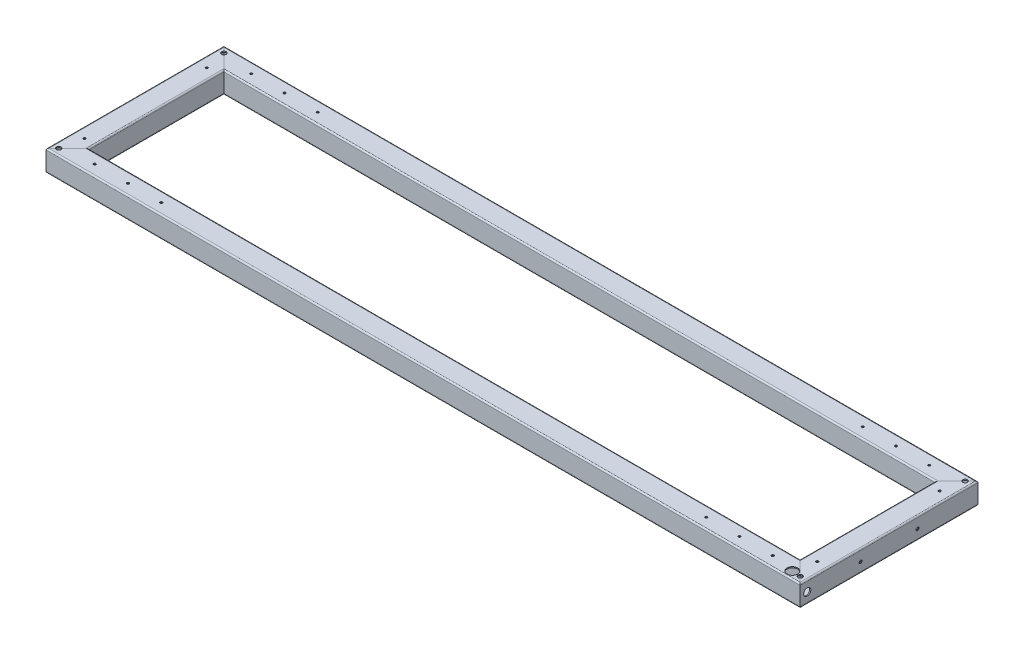
SolidWorks part; units mm, degrees
material "Unlegierter Baustahl"
ref_plane "Ebene vorne" through (0, 0, 0) normal (0, 0, 1) x (1, 0, 0)
ref_plane "Ebene oben" through (0, 0, 0) normal (0, 1, 0) x (1, 0, 0)
ref_plane "Ebene rechts" through (0, 0, 0) normal (1, 0, 0) x (0, 0, -1)
sketch "Skizze1" plane through (0, 0, 0) normal (0, 1, 0) x (1, 0, 0)
  line L1 (-1060, 250) -> (1060, 250)
  line L2 (-1060, 250) -> (-1060, -250)
  line L3 (-1060, -250) -> (1060, -250)
  line L4 (1060, 250) -> (1060, -250)
  line L5 (-1060, 250) -> (1060, -250) construction
  line L6 (-1060, -250) -> (1060, 250) construction
  point P0 (0, 0)
  dimension "D1" = 500
  dimension "D2" = 2120
other "Strukturbauteil1"
ref_plane "Ebene2" through (-1060, 0, -220) normal (1, 0, 0) x (0, 0, -1)
sketch "Skizze12" plane through (-1060, 0, -220) normal (1, 0, 0) x (0, 0, -1)
  line L0 (27, -26) -> (27, 26)
  line L1 (26, -30) -> (-26, -30)
  line L2 (30, -26) -> (30, 26)
  line L3 (26, 30) -> (-26, 30)
  line L4 (-30, -26) -> (-30, 26)
  line L5 (26, 27) -> (-26, 27)
  line L6 (-27, -26) -> (-27, 26)
  line L7 (26, -27) -> (-26, -27)
  line L8 (0, -30) -> (0, 30) construction
  arc A0 (-30, 26) -> (-26, 30) centre (-26, 26) cw
  arc A1 (-26, -30) -> (-30, -26) centre (-26, -26) cw
  arc A2 (30, -26) -> (26, -30) centre (26, -26) cw
  arc A3 (26, 30) -> (30, 26) centre (26, 26) cw
  arc A4 (26, 27) -> (27, 26) centre (26, 26) cw
  arc A5 (-27, 26) -> (-26, 27) centre (-26, 26) cw
  arc A6 (-26, -27) -> (-27, -26) centre (-26, -26) cw
  arc A7 (27, -26) -> (26, -27) centre (26, -26) cw
  point P4 (0, 30)
  point P5 (0, -30)
  point P10 (-30, -30)
  point P13 (30, -30)
  point P16 (30, 30)
  point P25 (-30, -30)
  point P26 (-30, 30)
  point P27 (30, 30)
  point P30 (30, -30)
  point P31 (0, 0)
  point P32 (-30, 0)
  point P33 (30, 0)
  point P34 (0, 0)
  dimension "D3" = 4
  dimension "D1" = 60
  dimension "D2" = 60
  dimension "D4" = 3
hole_wizard "M6 Gewindebohrung1" positions "Skizze16" profile "Skizze15" tap size "M6" standard "DIN" end condition up to next
sketch "Skizze16" plane through (0, 30, 0) normal (0, 1, 0) x (1, 0, 0)
  point P0 (1030, -172)
  point P3 (1030, 172)
sketch "Skizze15" plane through (1030, 30, 172) normal (1, 0, 0) x (0, 0, 1)
  line L0 (0, 0) -> (0, 3)
  line L1 (0, 3) -> (3.025, 3)
  line L2 (2.5, 2.475) -> (2.5, 0.75)
  line L3 (2.5, 0.75) -> (3.25, 0)
  line L5 (3.25, 0) -> (0, 0)
  line L6 (-2.5, 0.75) -> (-3.25, 0) construction
  line L7 (3.025, 3) -> (2.5, 2.475)
  line L8 (-3.025, 3) -> (-2.5, 2.475) construction
  line L11 (0, -6.35) -> (0, 107.95) construction
  dimension "Bohrerdurchmesser" = 5
  dimension "Bohrungstiefe" = 3
  dimension "Senkdurchmesser (Oben)" = 6.5
  dimension "Senkwinkel (Oben)" = 90
  dimension "Senkdurchmesser (Unten)" = 6.05
  dimension "Senkwinkel (Unten)" = 90
cosmetic thread "Bohrungsgewinde9" parameters "D2"=6
cosmetic thread "Bohrungsgewinde10" parameters "D2"=6
hole_wizard "M6 Gewindebohrung2" positions "Skizze18" profile "Skizze17" tap size "M6" standard "DIN" end condition up to next
sketch "Skizze18" plane through (0, 30, 0) normal (0, 1, 0) x (1, 0, 0)
  point P0 (-1030, 172)
  point P3 (-1030, -172)
sketch "Skizze17" plane through (-1030, 30, -172) normal (1, 0, 0) x (0, 0, 1)
  line L0 (0, 0) -> (0, 3)
  line L1 (0, 3) -> (3.025, 3)
  line L2 (2.5, 2.475) -> (2.5, 0.75)
  line L3 (2.5, 0.75) -> (3.25, 0)
  line L5 (3.25, 0) -> (0, 0)
  line L6 (-2.5, 0.75) -> (-3.25, 0) construction
  line L7 (3.025, 3) -> (2.5, 2.475)
  line L8 (-3.025, 3) -> (-2.5, 2.475) construction
  line L11 (0, -6.35) -> (0, 107.95) construction
  dimension "Bohrerdurchmesser" = 5
  dimension "Bohrungstiefe" = 3
  dimension "Senkdurchmesser (Oben)" = 6.5
  dimension "Senkwinkel (Oben)" = 90
  dimension "Senkdurchmesser (Unten)" = 6.05
  dimension "Senkwinkel (Unten)" = 90
cosmetic thread "Bohrungsgewinde11" parameters "D2"=6
cosmetic thread "Bohrungsgewinde12" parameters "D2"=6
sketch "Skizze19" plane through (0, 30, 0) normal (0, 1, 0) x (1, 0, 0)
  line L0 (-1060, -250) -> (1060, -250) construction
  line L1 (1060, -250) -> (1060, 250) construction
  circle A0 centre (1018, -230) radius 15
  dimension "D1" = 30
  dimension "D2" = 20
  dimension "D3" = 42
extrude "Schnitt-Linear austragen1" cut sketch "Skizze19" against normal up to next
sketch "Skizze20" plane through (0, 0, 190) normal (0, 0, -1) x (-1, 0, 0)
  line L0 (1004, 30) -> (-1004, 30) construction
  line L1 (-1000, -26) -> (-1000, 26) construction
  circle A0 centre (-670, 0) radius 15
  dimension "D1" = 30
  dimension "D2" = 30
  dimension "D3" = 330
extrude "Schnitt-Linear austragen2" cut sketch "Skizze20" against normal up to next
sketch "Skizze21" plane through (1060, 0, 0) normal (1, 0, 0) x (0, 0, -1)
  line L0 (-246, -30) -> (246, -30) construction
  line L1 (-250, 26) -> (-250, -26) construction
  circle A0 centre (-230, 0) radius 10
  dimension "D1" = 20
  dimension "D2" = 30
  dimension "D3" = 20
extrude "Schnitt-Linear austragen3" cut sketch "Skizze21" against normal up to next
sketch "Skizze22" plane through (0, -30, 0) normal (0, -1, 0) x (1, 0, 0)
  line L0 (1056, 0) -> (51056, 0) construction
  line L1 (1056, 246) -> (1056, -246) construction
  line L2 (1060, 250) -> (1060, -250) construction
  line L3 (-1000, -190) -> (-1000, 190) construction
  circle A0 centre (-1030, 0) radius 15
  circle A1 centre (1030, 0) radius 15
  point P8 (1056, 0)
  dimension "D1" = 30
  dimension "D2" = 30
  dimension "D3" = 30
extrude "Schnitt-Linear austragen4" cut sketch "Skizze22" against normal up to next
sketch "Skizze23" plane through (-1060, 0, 0) normal (-1, 0, 0) x (0, 0, 1)
  line L0 (-246, 30) -> (246, 30) construction
  line L1 (250, -26) -> (250, 26) construction
  circle A0 centre (230, 0) radius 10
  dimension "D1" = 20
  dimension "D2" = 30
  dimension "D3" = 20
extrude "Schnitt-Linear austragen5" cut sketch "Skizze23" against normal up to next
hole_wizard "M8 Gewindebohrung1" positions "Skizze25" profile "Skizze24" tap size "M8" standard "DIN" end condition up to next
sketch "Skizze25" plane through (1060, 0, 0) normal (1, 0, 0) x (0, 0, -1)
  point P0 (-80, -1.4975)
  point P3 (80, -1.4975)
sketch "Skizze24" plane through (1060, -1.4975, 80) normal (0, 1, 0) x (0, 0, -1)
  line L0 (0, 0) -> (0, 3)
  line L1 (0, 3) -> (3.4, 3)
  line L2 (3.4, 3) -> (3.4, 0.85)
  line L3 (3.4, 0.85) -> (4.25, 0)
  line L5 (4.25, 0) -> (0, 0)
  line L6 (-3.4, 0.85) -> (-4.25, 0) construction
  line L11 (0, -6.35) -> (0, 107.95) construction
  dimension "Bohrerdurchmesser" = 6.8
  dimension "Bohrungstiefe" = 3
  dimension "Senkdurchmesser (Oben)" = 8.5
  dimension "Senkwinkel (Oben)" = 90
cosmetic thread "Bohrungsgewinde14" parameters "D2"=8
cosmetic thread "Bohrungsgewinde15" parameters "D2"=8
sketch "Skizze26" plane through (0, 30, 0) normal (0, 1, 0) x (1, 0, 0)
  line L0 (-1056, -246) -> (-1004, -194) construction
  line L1 (-1060, -250) -> (1060, -250) construction
  line L2 (-1056, 246) -> (-1004, 194) construction
  line L3 (1004, 194) -> (1056, 246) construction
  line L4 (1004, -194) -> (1056, -246) construction
  line L5 (1060, 250) -> (-1060, 250) construction
  circle A0 centre (-1042, -232) radius 6.5
  circle A1 centre (-1042, 232) radius 6.5
  circle A2 centre (1042, 232) radius 6.5
  circle A3 centre (1042, -232) radius 6.5
  dimension "D1" = 13
  dimension "D2" = 18
  dimension "D3" = 18
  dimension "D4" = 18
  dimension "D5" = 18
extrude "Schnitt-Linear austragen6" cut sketch "Skizze26" against normal through all
hole_wizard "M6 Gewindebohrung3" positions "Skizze40" profile "Skizze41" tap size "M6" standard "DIN" end condition up to next
sketch "Skizze40" plane through (0, 30, 0) normal (0, 1, 0) x (1, 0, 0)
  point P0 (-953, 220)
  point P3 (-859.5, 220)
  point P6 (-766, 220)
  point P9 (766, 220)
  point P12 (859.5, 220)
  point P15 (953, 220)
  point P18 (766, -220)
  point P21 (859.5, -220)
  point P24 (953, -220)
  point P27 (-953, -220)
  point P30 (-859.5, -220)
  point P33 (-766, -220)
sketch "Skizze41" plane through (-953, 30, -220) normal (1, 0, 0) x (0, 0, 1)
  line L0 (0, 0) -> (0, 3)
  line L1 (0, 3) -> (2.5, 3)
  line L2 (2.5, 3) -> (2.5, 0.75)
  line L3 (2.5, 0.75) -> (3.25, 0)
  line L5 (3.25, 0) -> (0, 0)
  line L6 (-2.5, 0.75) -> (-3.25, 0) construction
  line L11 (0, -6.35) -> (0, 107.95) construction
  dimension "Bohrerdurchmesser" = 5
  dimension "Bohrungstiefe" = 3
  dimension "Senkdurchmesser (Oben)" = 6.5
  dimension "Senkwinkel (Oben)" = 90
cosmetic thread "Bohrungsgewinde16" parameters "D2"=6
cosmetic thread "Bohrungsgewinde17" parameters "D2"=6
cosmetic thread "Bohrungsgewinde18" parameters "D2"=6
cosmetic thread "Bohrungsgewinde19" parameters "D2"=6
cosmetic thread "Bohrungsgewinde20" parameters "D2"=6
cosmetic thread "Bohrungsgewinde21" parameters "D2"=6
cosmetic thread "Bohrungsgewinde22" parameters "D2"=6
cosmetic thread "Bohrungsgewinde23" parameters "D2"=6
cosmetic thread "Bohrungsgewinde24" parameters "D2"=6
cosmetic thread "Bohrungsgewinde25" parameters "D2"=6
cosmetic thread "Bohrungsgewinde26" parameters "D2"=6
cosmetic thread "Bohrungsgewinde27" parameters "D2"=6
